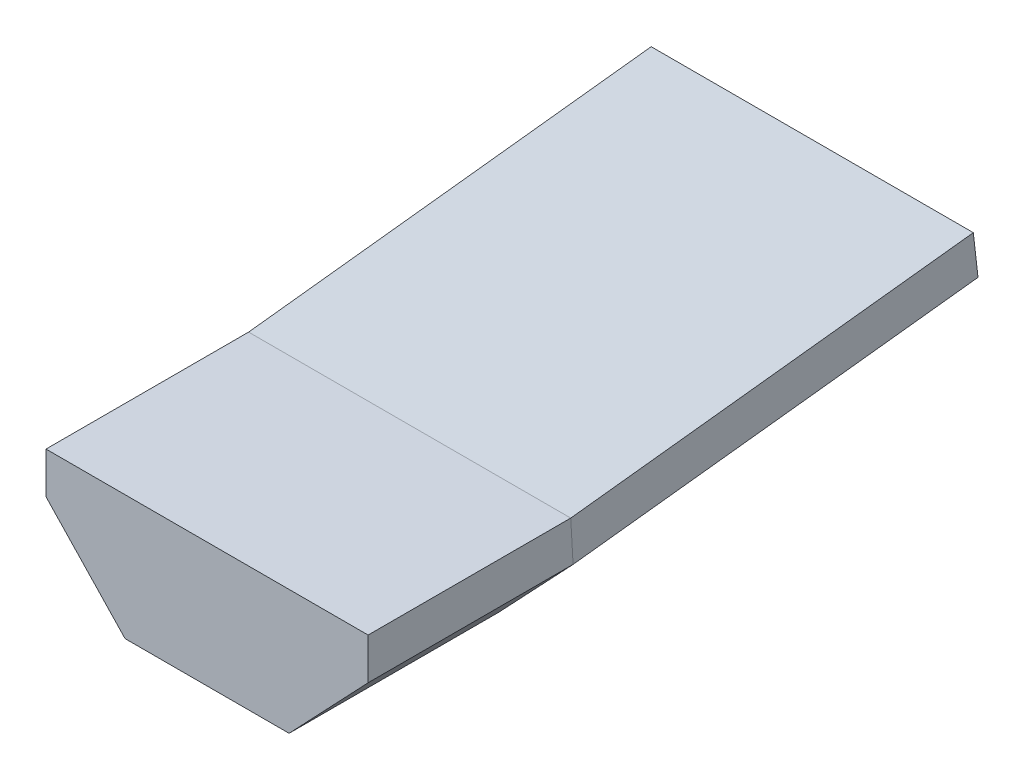
SolidWorks part; units mm, degrees
ref_plane "Front Plane" through (0, 0, 0) normal (0, 0, 1) x (1, 0, 0)
ref_plane "Top Plane" through (0, 0, 0) normal (0, 1, 0) x (1, 0, 0)
ref_plane "Right Plane" through (0, 0, 0) normal (1, 0, 0) x (0, 0, -1)
sketch "Sketch1" plane through (0, 0, 0) normal (0, 0, 1) x (1, 0, 0)
  line B0 (7.95, 0) -> (7.95, -2.04)
  line B1 (4.048, -6.1524) -> (-4.048, -6.1524)
  line B2 (-7.95, -2.04) -> (-7.95, 0)
  line B3 (-7.95, 0) -> (7.95, 0)
  line B4 (7.95, -2.04) -> (4.048, -6.1524)
  line B5 (-4.048, -6.1524) -> (-7.95, -2.04)
sketch_block_instance "Extrusion Profile-2"
sketch_block "Extrusion Profile" parameters "D1"=8.44, "D2"=2.6, "D3"=6, "D4"=16.7, "D6"=5.6686, "D7"=2.0404, "D8"=8.0963, "D9"=15.9, "D5"=2.4157
sketch "Sketch2" plane through (0, 0, 0) normal (1, 0, 0) x (0, 0, -1)
  line L0 (0, 0) -> (10, 0)
  line L1 (10, 0) -> (29.8714, 2.2641)
  dimension "D1" = 173.5
  dimension "D2" = 10
  dimension "D3" = 20
sweep "Sweep1" add profiles "Sketch1" path "Sketch2"
